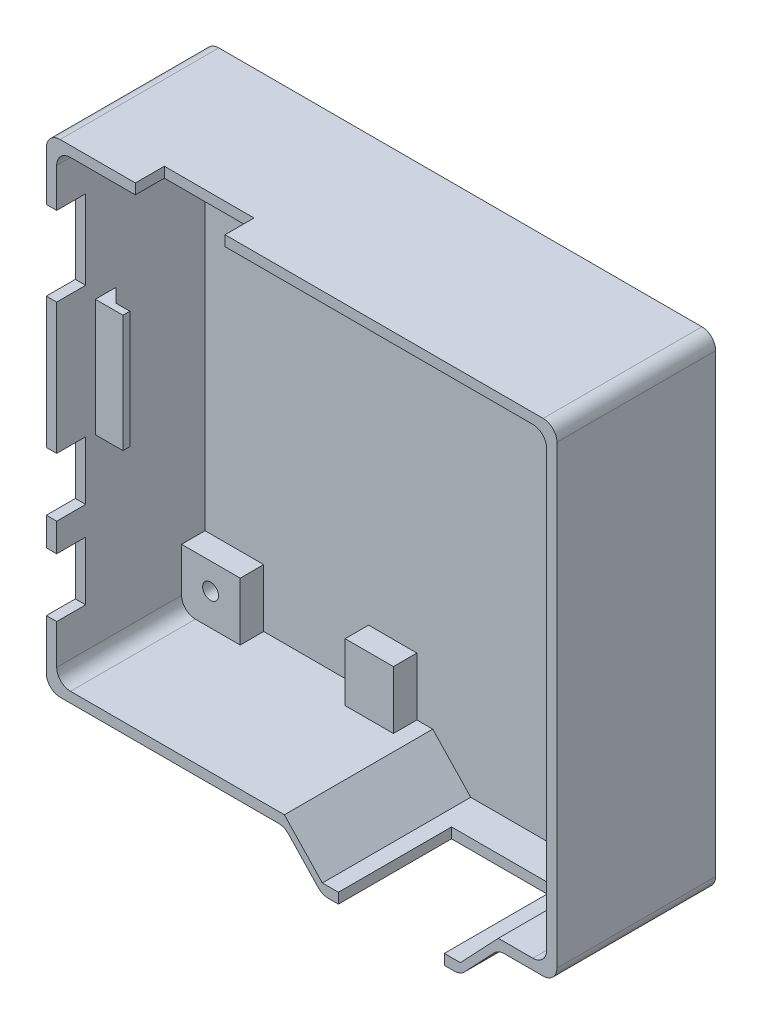
SolidWorks part; units mm, degrees
ref_plane "Plan de face" through (0, 0, 0) normal (0, 0, 1) x (1, 0, 0)
ref_plane "Plan de dessus" through (0, 0, 0) normal (0, 1, 0) x (1, 0, 0)
ref_plane "Plan de droite" through (0, 0, 0) normal (1, 0, 0) x (0, 0, -1)
sketch "Esquisse1" plane through (0, 0, 0) normal (0, 0, 1) x (1, 0, 0)
  line L0 (-2.5, -35) -> (3, -40.8095)
  line L1 (-37, 35) -> (37, 35)
  line L2 (-37, 35) -> (-37, -35)
  line L3 (-37, -35) -> (-2.5, -35)
  line L4 (37, 35) -> (37, -35)
  line L5 (-37, 35) -> (37, -35) construction
  line L6 (-37, -35) -> (37, 35) construction
  line L7 (3, -40.8095) -> (23, -40.8095)
  line L8 (23, -40.8095) -> (28.5, -35)
  line L9 (28.5, -35) -> (37, -35)
  point P0 (0, 0)
  dimension "D1" = 74
  dimension "D2" = 70
  dimension "D3" = 20
  dimension "D4" = 8.5
  dimension "D5" = 34.5
  dimension "D6" = 8
extrude "Boss.-Extru.1" add sketch "Esquisse1" along normal blind 23
sketch "Esquisse2" plane through (0, 0, 23) normal (0, 0, 1) x (1, 0, 0)
  line L0 (-2.5, -33.5) -> (3, -39.3095)
  line L1 (-35.5, 33.5) -> (35.5, 33.5)
  line L2 (-35.5, 33.5) -> (-35.5, -33.5)
  line L3 (-35.5, -33.5) -> (-2.5, -33.5)
  line L4 (35.5, 33.5) -> (35.5, -33.5)
  line L5 (-35.5, 33.5) -> (35.5, -33.5) construction
  line L6 (-35.5, -33.5) -> (35.5, 33.5) construction
  line L7 (3, -39.3095) -> (23, -39.3095)
  line L8 (23, -39.3095) -> (28.5, -33.5)
  line L9 (28.5, -33.5) -> (35.5, -33.5)
  line L10 (37, 35) -> (-37, 35) construction
  line L11 (37, -35) -> (37, 35) construction
  line L13 (3, -40.8095) -> (23, -40.8095) construction
  point P0 (0, 0)
  dimension "D1" = 1.5
  dimension "D2" = 1.5
  dimension "D3" = 7
  dimension "D4" = 33
  dimension "D5" = 8
extrude "Enlèv. mat.-Extru.1" cut sketch "Esquisse2" against normal blind 21.5
sketch "Esquisse3" plane through (0, 0, 1.5) normal (0, 0, 1) x (1, 0, 0)
  line L0 (0, -12.65) -> (0, 12.65) construction
  line L1 (35.5, 33.5) -> (27, 33.5)
  line L2 (35.5, 33.5) -> (35.5, 25.1)
  line L3 (35.5, 25.1) -> (27, 25.1)
  line L4 (27, 33.5) -> (27, 25.1)
  line L5 (-35.5, 25.1) -> (-27, 25.1)
  line L6 (-27, 33.5) -> (-27, 25.1)
  line L7 (-35.5, 33.5) -> (-27, 33.5)
  line L8 (-35.5, 33.5) -> (-35.5, 25.1)
  line L9 (12.65, 0) -> (-12.65, 0) construction
  line L10 (35.5, -25.1) -> (27, -25.1)
  line L11 (27, -33.5) -> (27, -25.1)
  line L12 (35.5, -33.5) -> (27, -33.5)
  line L13 (35.5, -33.5) -> (35.5, -25.1)
  line L14 (-35.5, -33.5) -> (-35.5, -25.1)
  line L15 (-35.5, -33.5) -> (-27, -33.5)
  line L16 (-27, -33.5) -> (-27, -25.1)
  line L17 (-35.5, -25.1) -> (-27, -25.1)
  dimension "D1" = 8.4
  dimension "D2" = 8.5
extrude "Boss.-Extru.3" add sketch "Esquisse3" along normal blind 3.4
sketch "Esquisse4" plane through (0, -33.5, 0) normal (0, -1, 0) x (1, 0, 0)
  line L1 (27, 4.9) -> (28.5, 4.9)
  line L2 (27, 4.9) -> (27, 1.4934)
  line L3 (27, 1.4934) -> (28.5, 1.4934)
  line L4 (28.5, 4.9) -> (28.5, 1.4934)
extrude "Boss.-Extru.5" add sketch "Esquisse4" along normal up to next
sketch "Esquisse23" plane through (0, 0, 4.9) normal (0, 0, 1) x (1, 0, 0)
  line L0 (35.5, 33.5) -> (27, 33.5) construction
  line L1 (35.5, 25.1) -> (35.5, 33.5) construction
  line L2 (0, -12.65) -> (0, 12.65) construction
  circle A0 centre (31.3, 29.3) radius 1.15
  circle A1 centre (-31.3, 29.3) radius 1.15
  circle A4 centre (31.3, -28.9) radius 1.15
  circle A5 centre (-31.3, -28.9) radius 1.15
  dimension "D1" = 2.3
  dimension "D2" = 4.2
  dimension "D3" = 4.2
  dimension "D4" = 2
extrude "Enlèv. mat.-Extru.2" cut sketch "Esquisse23" against normal blind 4
sketch "Esquisse24" plane through (0, 0, 1.5) normal (0, 0, 1) x (1, 0, 0)
  line L0 (27, 33.5) -> (-27, 33.5) construction
  line L1 (-11.8, 33.5) -> (-4.8, 33.5)
  line L2 (-11.8, 33.5) -> (-11.8, 25.1)
  line L3 (-11.8, 25.1) -> (-4.8, 25.1)
  line L4 (-4.8, 33.5) -> (-4.8, 25.1)
  line L5 (12.65, 0) -> (-12.65, 0) construction
  line L6 (-11.8, -25.1) -> (-4.8, -25.1)
  line L7 (-4.8, -33.5) -> (-4.8, -25.1)
  line L8 (-11.8, -33.5) -> (-4.8, -33.5)
  line L9 (-11.8, -33.5) -> (-11.8, -25.1)
  circle A0 centre (-31.3, 29.3) radius 1.15 construction
  dimension "D1" = 19.5
  dimension "D2" = 7
  dimension "D3" = 8.4
extrude "Boss.-Extru.6" add sketch "Esquisse24" along direction (0, 0, 1) on the side of the normal up to surface (3.4 mm away)
sketch "Esquisse26" plane through (0, -40.8095, 0) normal (0, -1, 0) x (1, 0, 0)
  line L0 (3, 23) -> (23, 23) construction
  line L1 (5.325, 23) -> (20.675, 23)
  line L2 (5.325, 23) -> (5.325, 6.6)
  line L3 (5.325, 6.6) -> (20.675, 6.6)
  line L4 (20.675, 23) -> (20.675, 6.6)
  line L5 (3, 0) -> (23, 0) construction
  point P8 (13, 23)
  point P9 (13, 23)
  dimension "D1" = 6.6
  dimension "D2" = 15.35
extrude "Enlèv. mat.-Extru.4" cut sketch "Esquisse26" against normal up to next
sketch "Esquisse27" plane through (-35.5, 0, 0) normal (1, 0, 0) x (0, 0, -1)
  line L0 (-23, 35) -> (0, 35) construction
  line L1 (-16.4, 11.9) -> (-17.4, 11.9)
  line L2 (-16.4, 11.9) -> (-16.4, -5.1)
  line L3 (-16.4, -5.1) -> (-17.4, -5.1)
  line L4 (-17.4, 11.9) -> (-17.4, -5.1)
  line L6 (-4.9, 33.5) -> (-4.9, 25.1) construction
  dimension "D1" = 23.1
  dimension "D2" = 11.5
  dimension "D3" = 1
  dimension "D4" = 17
extrude "Boss.-Extru.7" add sketch "Esquisse27" along normal blind 4
chamfer "Chanfrein1" distance 2 angle 45 1 edges at (-35.5, 3.4, 16.4)
sketch "Esquisse28" plane through (-37, 0, 0) normal (-1, 0, 0) x (0, 0, 1)
  line L0 (23, 35) -> (23, -35) construction
  line L1 (23, 25.85) -> (18.8, 25.85)
  line L2 (23, 25.85) -> (23, 14.35)
  line L3 (23, 14.35) -> (18.8, 14.35)
  line L4 (18.8, 25.85) -> (18.8, 14.35)
  line L5 (23, 35) -> (0, 35) construction
  line L6 (17.4, 11.9) -> (17.4, -5.1) construction
  point P6 (18.8, 20.1)
  dimension "D1" = 14.9
  dimension "D2" = 11.5
  dimension "D3" = 1.4
extrude "Enlèv. mat.-Extru.5" cut sketch "Esquisse28" against normal up to next
sketch "Esquisse29" plane through (-37, 0, 0) normal (-1, 0, 0) x (0, 0, 1)
  line L0 (23, 14.35) -> (23, -35) construction
  line L1 (23, -4.65) -> (18.8, -4.65)
  line L2 (23, -4.65) -> (23, -13.15)
  line L3 (23, -13.15) -> (18.8, -13.15)
  line L4 (18.8, -4.65) -> (18.8, -13.15)
  line L5 (23, 35) -> (0, 35) construction
  line L6 (17.4, 11.9) -> (17.4, -5.1) construction
  line L7 (23, -17.25) -> (23, -25.75)
  line L8 (23, -17.25) -> (18.8, -17.25)
  line L9 (18.8, -17.25) -> (18.8, -25.75)
  line L10 (23, -25.75) -> (18.8, -25.75)
  point P6 (18.8, -8.9)
  dimension "D1" = 43.9
  dimension "D2" = 8.5
  dimension "D3" = 1.4
  dimension "D4" = 2
extrude "Enlèv. mat.-Extru.6" cut sketch "Esquisse29" against normal up to next
sketch "Esquisse30" plane through (0, 35, 0) normal (0, 1, 0) x (1, 0, 0)
  line L0 (37, -23) -> (-37, -23) construction
  line L1 (-24.1, -23) -> (-11.1, -23)
  line L2 (-24.1, -23) -> (-24.1, -18.8)
  line L3 (-24.1, -18.8) -> (-11.1, -18.8)
  line L4 (-11.1, -23) -> (-11.1, -18.8)
  line L5 (-37, -23) -> (-37, 0) construction
  line L6 (-31.5, -17.4) -> (-35.5, -17.4) construction
  point P6 (-17.6, -18.8)
  dimension "D1" = 19.4
  dimension "D2" = 13
  dimension "D3" = 1.4
extrude "Enlèv. mat.-Extru.8" cut sketch "Esquisse30" against normal blind 4
fillet "Congé1" radius 2 12 edges at (-37, 35, 11.5) (37, 35, 11.5) (37, -35, 11.5) (-37, -35, 11.5) (-35.5, -33.5, 13.95) (35.5, -33.5, 13.95) (35.5, 33.5, 13.95) (-35.5, 33.5, 13.95) (23, -40.8095, 11.5) (3, -40.8095, 11.5) (28.5, -35, 11.5) (-2.5, -35, 11.5)
